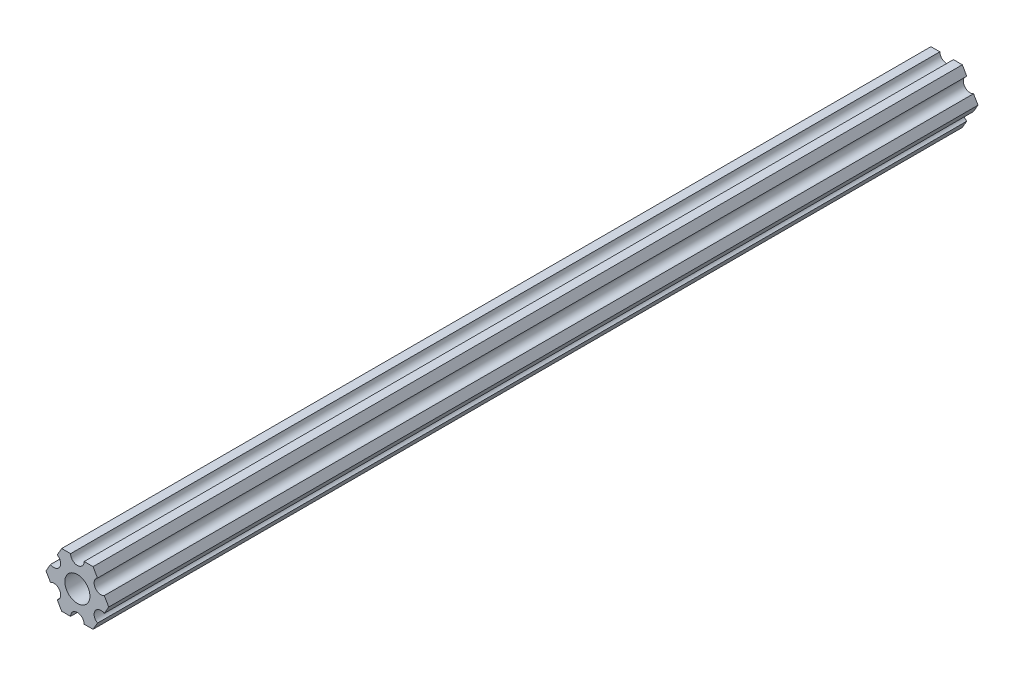
SolidWorks part; units mm, degrees
material "6061-T6 (SS)"
ref_plane "Front Plane" through (0, 0, 0) normal (0, 0, 1) x (1, 0, 0)
ref_plane "Top Plane" through (0, 0, 0) normal (0, 1, 0) x (1, 0, 0)
ref_plane "Right Plane" through (0, 0, 0) normal (1, 0, 0) x (0, 0, -1)
sketch "Sketch1" plane through (0, 0, 0) normal (0, 0, 1) x (1, 0, 0)
  line L0 (-4.7055, -4.5498) -> (-3.6662, -6.35)
  line L1 (-3.6662, -6.35) -> (-1.5875, -6.35)
  line L2 (1.5875, -6.35) -> (3.6662, -6.35)
  line L3 (3.6662, -6.35) -> (4.7055, -4.5498)
  line L4 (6.293, -1.8002) -> (7.3323, 0)
  line L5 (7.3323, 0) -> (6.293, 1.8002)
  line L6 (4.7055, 4.5498) -> (3.6662, 6.35)
  line L7 (3.6662, 6.35) -> (1.5875, 6.35)
  line L8 (-1.5875, 6.35) -> (-3.6662, 6.35)
  line L9 (-3.6662, 6.35) -> (-4.7055, 4.5498)
  line L10 (-6.293, 1.8002) -> (-7.3323, 0)
  line L11 (-7.3323, 0) -> (-6.293, -1.8002)
  circle A0 centre (0, 0) radius 2.9337
  arc A1 (-6.293, -1.8002) -> (-4.7055, -4.5498) centre (-5.4993, -3.175) cw
  arc A2 (-1.5875, -6.35) -> (1.5875, -6.35) centre (0, -6.35) cw
  arc A3 (4.7055, -4.5498) -> (6.293, -1.8002) centre (5.4993, -3.175) cw
  arc A4 (6.293, 1.8002) -> (4.7055, 4.5498) centre (5.4993, 3.175) cw
  arc A5 (1.5875, 6.35) -> (-1.5875, 6.35) centre (0, 6.35) cw
  arc A6 (-4.7055, 4.5498) -> (-6.293, 1.8002) centre (-5.4993, 3.175) cw
extrude "Boss-Extrude1" add sketch "Sketch1" against normal blind 203.2
